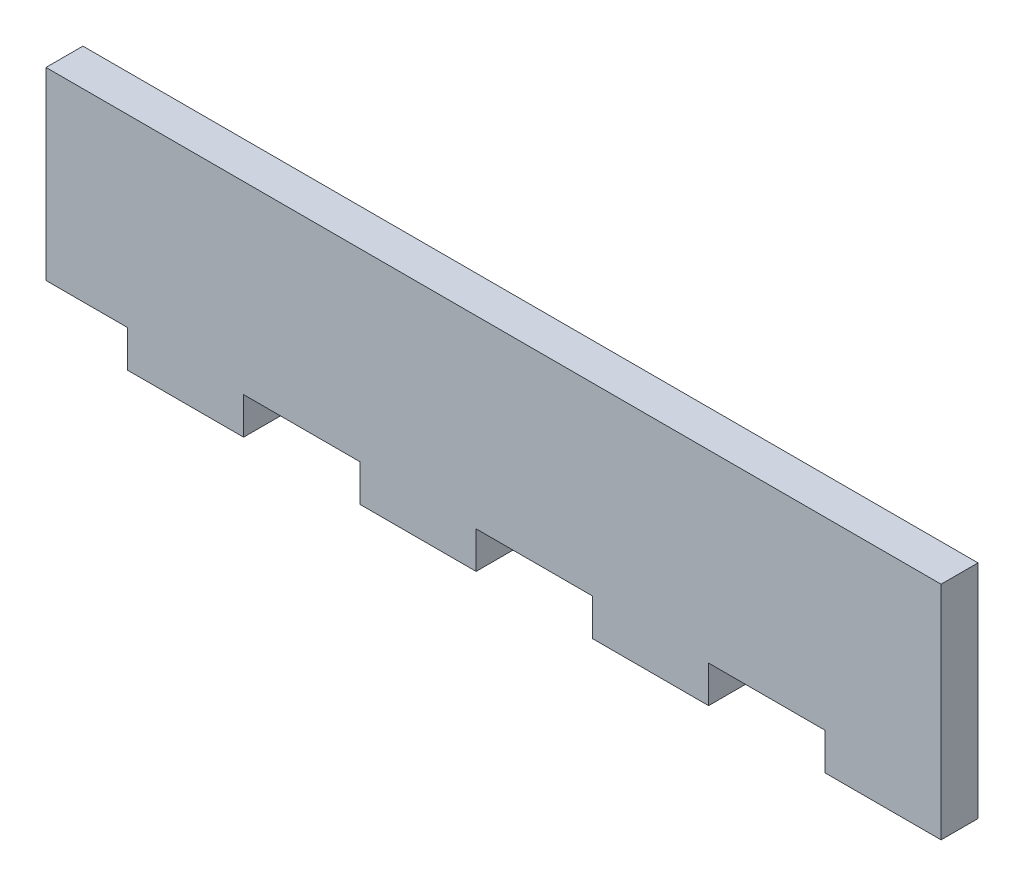
SolidWorks part; units mm, degrees
ref_plane "Front Plane" through (0, 0, 0) normal (0, 0, 1) x (1, 0, 0)
ref_plane "Top Plane" through (0, 0, 0) normal (0, 1, 0) x (1, 0, 0)
ref_plane "Right Plane" through (0, 0, 0) normal (1, 0, 0) x (0, 0, -1)
sketch "Sketch1" plane through (0, 0, 0) normal (1, 0, 0) x (0, 0, -1)
  line L1 (-2.1519, 0) -> (1.0231, 0)
  line L2 (-2.1519, 0) -> (-2.1519, 15.875)
  line L3 (-2.1519, 15.875) -> (1.0231, 15.875)
  line L4 (1.0231, 0) -> (1.0231, 15.875)
  dimension "D1" = 3.175
  dimension "D2" = 15.875
extrude "Boss-Extrude1" add sketch "Sketch1" along normal blind 77
sketch "Sketch2" plane through (0, 0, -1.0231) normal (0, 0, -1) x (-1, 0, 0)
  line L0 (-57, 0) -> (-57, -3.175)
  line L1 (-77, 0) -> (-67, 0)
  line L2 (-77, 0) -> (-77, -3.175)
  line L3 (-77, -3.175) -> (-67, -3.175)
  line L4 (-67, 0) -> (-67, -3.175)
  line L5 (-57, 0) -> (-47, 0)
  line L6 (-57, -3.175) -> (-47, -3.175)
  line L7 (-47, 0) -> (-47, -3.175)
  line L8 (-37, 0) -> (-37, -3.175)
  line L9 (-37, 0) -> (-27, 0)
  line L10 (-37, -3.175) -> (-27, -3.175)
  line L11 (-27, 0) -> (-27, -3.175)
  line L12 (-17, 0) -> (-17, -3.175)
  line L13 (-17, 0) -> (-7, 0)
  line L14 (-17, -3.175) -> (-7, -3.175)
  line L15 (-7, 0) -> (-7, -3.175)
  dimension "D1" = 3.175
  dimension "D2" = 10
  dimension "D3" = 4
extrude "Boss-Extrude2" add sketch "Sketch2" against normal blind 3.175
